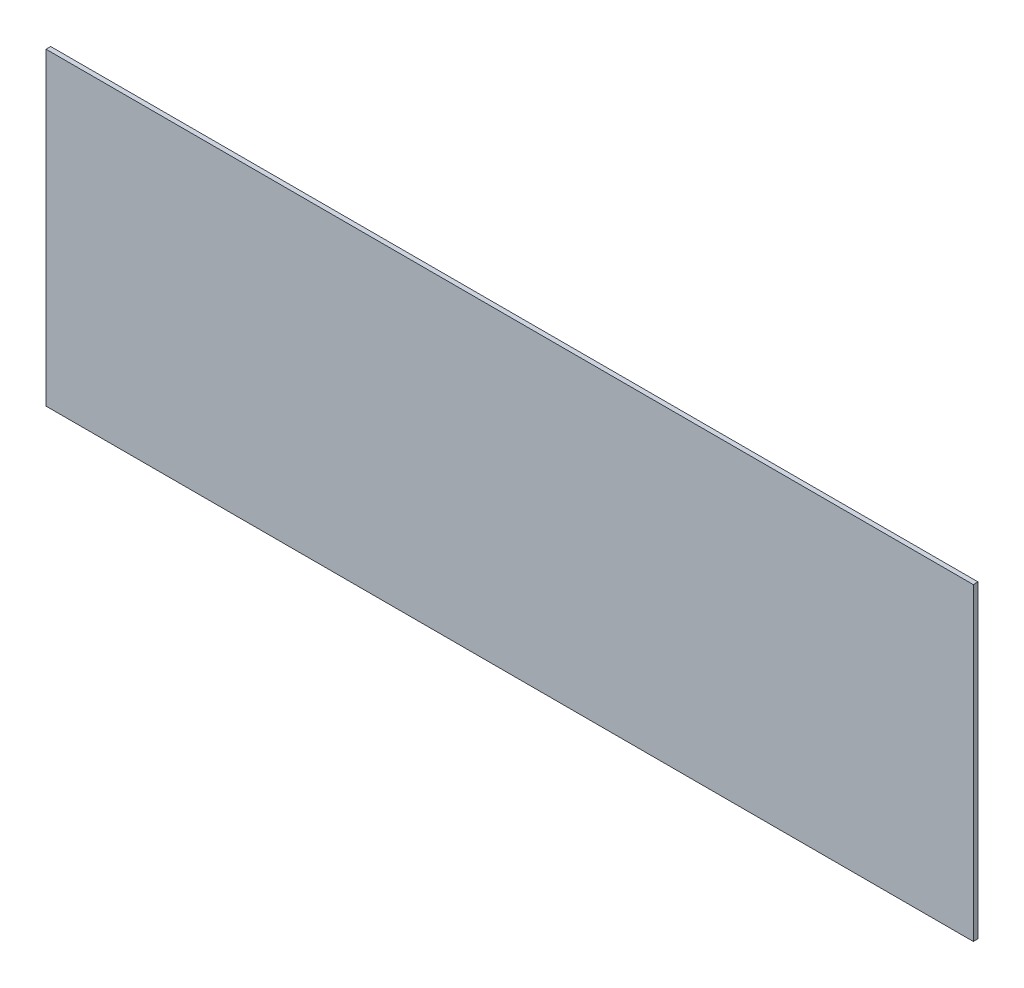
SolidWorks part; units mm, degrees
ref_plane "Front Plane" through (0, 0, 0) normal (0, 0, 1) x (1, 0, 0)
ref_plane "Top Plane" through (0, 0, 0) normal (0, 1, 0) x (1, 0, 0)
ref_plane "Right Plane" through (0, 0, 0) normal (1, 0, 0) x (0, 0, -1)
sketch "Sketch1" plane through (0, 0, 230.3482) normal (0, 0, -1) x (-1, 0, 0)
  line L1 (-2251.3398, 470.5234) -> (-994.0398, 470.5234)
  line L2 (-2251.3398, 470.5234) -> (-2251.3398, 51.4234)
  line L3 (-2251.3398, 51.4234) -> (-994.0398, 51.4234)
  line L4 (-994.0398, 470.5234) -> (-994.0398, 51.4234)
extrude "Boss-Extrude1" add sketch "Sketch1" along normal blind 6.35
